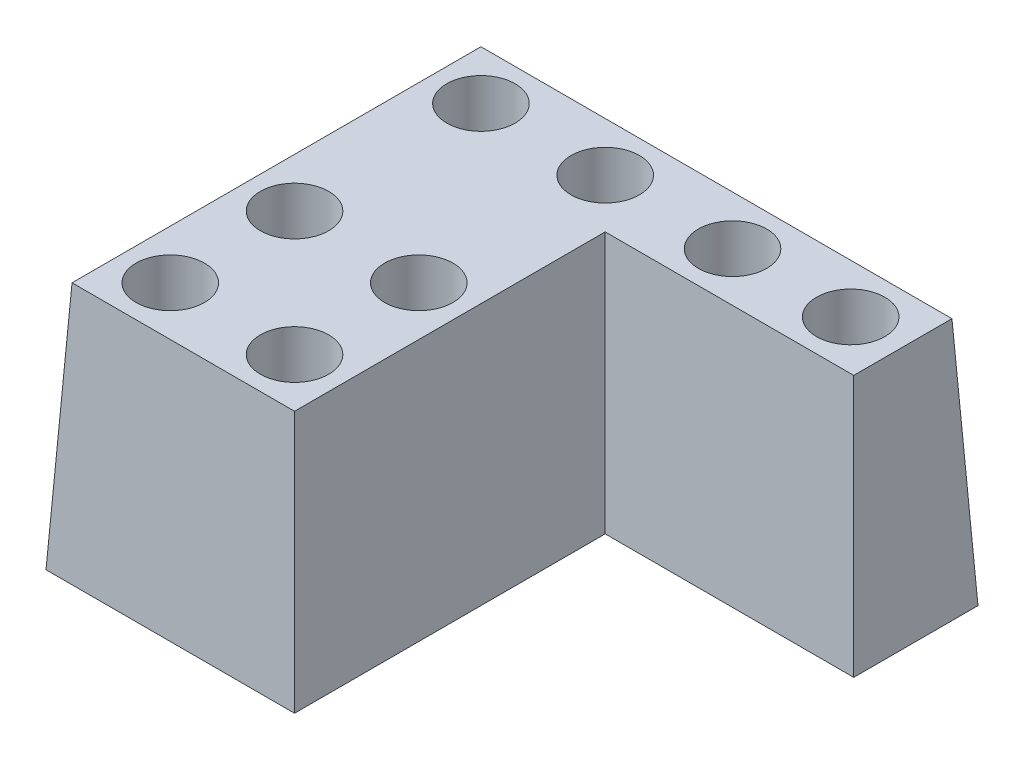
SolidWorks part; units mm, degrees
ref_plane "Front Plane" through (0, 0, 0) normal (0, 0, 1) x (1, 0, 0)
ref_plane "Top Plane" through (0, 0, 0) normal (0, 1, 0) x (1, 0, 0)
ref_plane "Right Plane" through (0, 0, 0) normal (1, 0, 0) x (0, 0, -1)
sketch "Sketch1" plane through (0, 0, 0) normal (0, 1, 0) x (1, 0, 0)
  line L0 (102.2951, 60) -> (-20, 60) construction
  line L1 (0, 0) -> (40, 0)
  line L2 (0, 0) -> (0, 70)
  line L3 (0, 70) -> (80, 70)
  line L4 (80, 50) -> (80, 70)
  line L5 (10, 79.3443) -> (10, -13.7705) construction
  line L8 (80, 50) -> (40, 50)
  line L9 (40, 0) -> (40, 50)
  line L10 (30, 79.3443) -> (30, -14.2623) construction
  line L11 (69.5082, 76.2295) -> (69.5082, 42.7869) construction
  line L12 (50.4918, 78.1967) -> (50.4918, 42.7869) construction
  line L13 (48.3607, 10) -> (-28.0328, 10) construction
  line L14 (46.7213, 30) -> (-25.5738, 30) construction
  dimension "D1" = 70
  dimension "D2" = 10
  dimension "D3" = 40
  dimension "D4" = 50
  dimension "D5" = 10
  dimension "D6" = 20
  dimension "D7" = 10
  dimension "D8" = 20
extrude "Boss-Extrude1" add sketch "Sketch1" along normal blind 40 draft 3
hole_wizard "CBORE for M5 SBHCS1" positions "Sketch2" profile "Sketch3" counterbore size "M5" standard "ANSI Metric" end condition through all
sketch "Sketch2" plane through (0, 40, 0) normal (0, 1, 0) x (1, 0, 0)
  line L0 (102.2951, 60) -> (-20, 60) construction
  line L1 (69.5082, 76.2295) -> (69.5082, 42.7869) construction
  line L2 (30, 79.3443) -> (30, -14.2623) construction
  line L3 (48.3607, 10) -> (-28.0328, 10) construction
  line L4 (10, 79.3443) -> (10, -13.7705) construction
  line L5 (50.4918, 78.1967) -> (50.4918, 42.7869) construction
  line L6 (46.7213, 30) -> (-25.5738, 30) construction
  point P0 (69.5082, 60)
  point P6 (30, 10)
  point P12 (10, 10)
  point P16 (10, 60)
  point P18 (50.4918, 60)
  point P22 (30, 60)
  point P24 (10, 30)
  point P28 (30, 30)
sketch "Sketch3" plane through (69.5082, 40, -60) normal (1, 0, 0) x (0, 0, 1)
  line L0 (0, 0) -> (0, 40)
  line L1 (0, 40) -> (2.75, 40)
  line L3 (2.75, 40) -> (2.75, 35)
  line L4 (2.75, 35) -> (5.5, 35)
  line L5 (5.5, 35) -> (5.5, 0)
  line L7 (5.5, 0) -> (0, 0)
  line L11 (0, -6.35) -> (0, 107.95) construction
  dimension "Thru Hole Dia." = 5.5
  dimension "Thru Hole Depth" = 40
  dimension "C'Bore Dia." = 11
  dimension "C'Bore Depth" = 35
move or copy body "Body-Move/Copy1" [suppressed] bodies to move or copy 102
